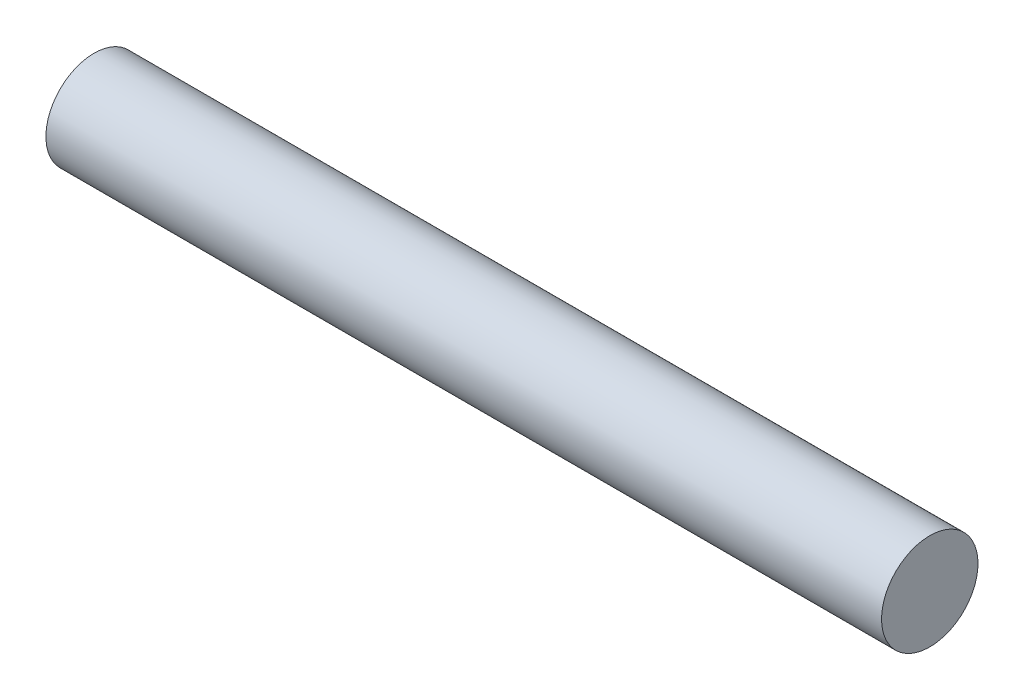
SolidWorks part; units mm, degrees
ref_plane "Alzado" through (0, 0, 0) normal (0, 0, 1) x (1, 0, 0)
ref_plane "Planta" through (0, 0, 0) normal (0, 1, 0) x (1, 0, 0)
ref_plane "Vista lateral" through (0, 0, 0) normal (1, 0, 0) x (0, 0, -1)
sketch "Croquis1" plane through (0, 0, 0) normal (0, 0, 1) x (1, 0, 0)
  line L0 (0, 0) -> (165.1, 0)
  point P3 (0, 0)
  dimension "D1" = 165.1
sketch "Croquis2" plane through (0, 0, 0) normal (1, 0, 0) x (0, 0, -1)
  circle A0 centre (0, 0) radius 9.525
  dimension "D1" = 19.05
sweep "Barrer1" add profiles "Croquis2" path "Croquis1"
ref_plane "Plano1" through (82.55, 0, 0) normal (1, 0, 0) x (0, 0, -1)
